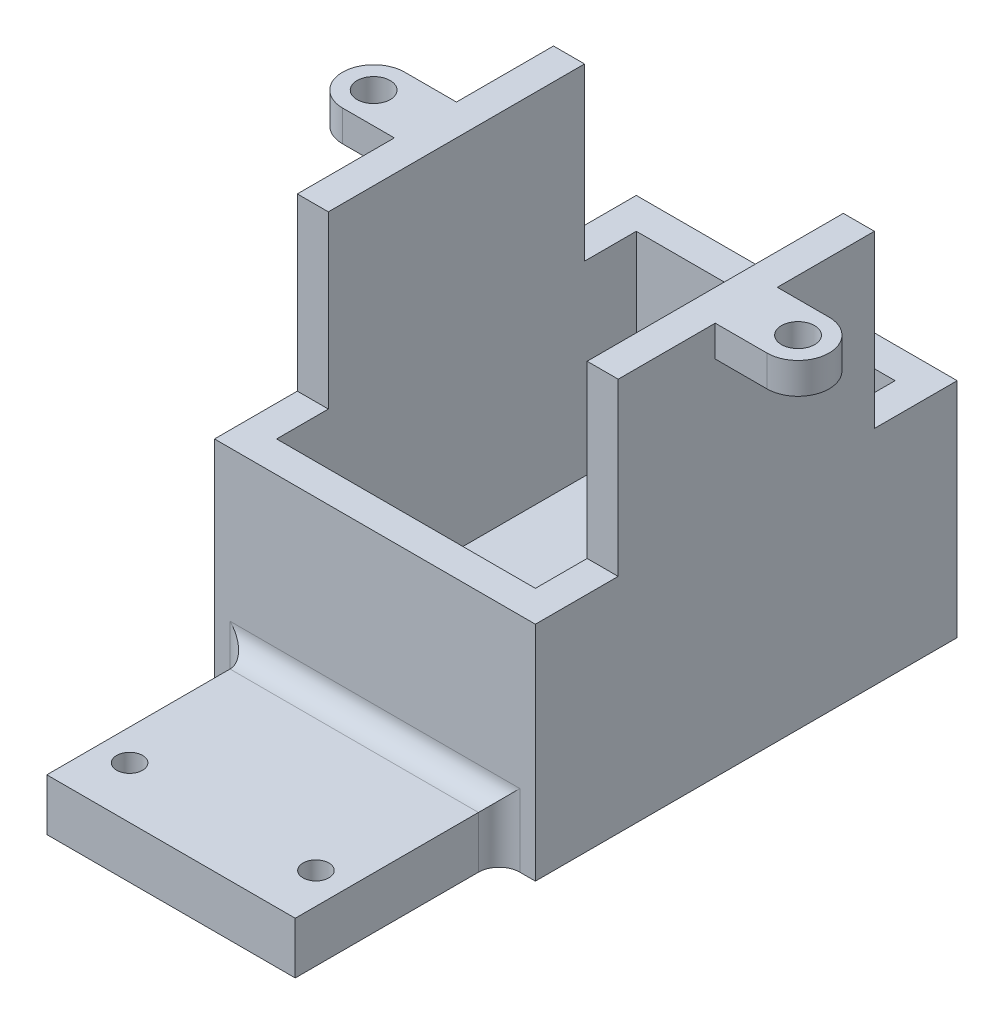
SolidWorks part; units mm, degrees
ref_plane "前视基准面" through (0, 0, 0) normal (0, 0, 1) x (1, 0, 0)
ref_plane "上视基准面" through (0, 0, 0) normal (0, 1, 0) x (1, 0, 0)
ref_plane "右视基准面" through (0, 0, 0) normal (1, 0, 0) x (0, 0, -1)
sketch "草图1" plane through (0, 0, 0) normal (0, 0, 1) x (1, 0, 0)
  line L1 (0, 0) -> (31, 0)
  line L2 (0, 0) -> (0, 38)
  line L3 (0, 38) -> (31, 38)
  line L4 (31, 0) -> (31, 38)
  dimension "D1" = 38
  dimension "D2" = 31
extrude "凸台-拉伸1" add sketch "草图1" against normal blind 40.75
sketch "草图2" plane through (31, 0, 0) normal (1, 0, 0) x (0, 0, -1)
  line L1 (40.75, 38) -> (32.75, 38)
  line L2 (40.75, 38) -> (40.75, 21.5)
  line L3 (40.75, 21.5) -> (32.75, 21.5)
  line L4 (32.75, 38) -> (32.75, 21.5)
  dimension "D1" = 16.5
  dimension "D2" = 8
extrude "切除-拉伸1" cut sketch "草图2" against normal blind 40.75
sketch "草图3" plane through (0, 38, 0) normal (0, 1, 0) x (1, 0, 0)
  line L0 (0, 40.75) -> (31, 0) construction
  line L1 (31, 40.75) -> (0, 40.75) construction
  line L2 (3, 3) -> (28, 3)
  line L3 (3, 3) -> (3, 37.75)
  line L4 (3, 37.75) -> (28, 37.75)
  line L5 (28, 3) -> (28, 37.75)
  line L6 (15.5, 37.75) -> (15.5, 3) construction
  line L7 (3, 20.375) -> (28, 20.375) construction
  line L8 (31, 32.75) -> (31, 0) construction
  point P4 (15.5, 20.375)
  dimension "D1" = 3
  dimension "D2" = 3
extrude "切除-拉伸2" cut sketch "草图3" against normal blind 34.5
sketch "草图4" plane through (0, 0, 0) normal (0, 0, 1) x (1, 0, 0)
  line L0 (31, 38) -> (0, 38) construction
  circle A0 centre (15.5, 38) radius 12.5
  dimension "D1" = 25
extrude "切除-拉伸3" cut sketch "草图4" against normal blind 34.5
sketch "草图5" plane through (0, 38, 0) normal (0, 1, 0) x (1, 0, 0)
  line L0 (0, 40.75) -> (31, 0) construction
  line L1 (15.5, 20.375) -> (15.5, 40.75) construction
  line L2 (15.5, 20.375) -> (31, 20.375) construction
  line L3 (31, 32.75) -> (31, 0) construction
  line L4 (36, 23.375) -> (31, 23.375)
  line L5 (31, 23.375) -> (31, 17.375)
  line L6 (31, 17.375) -> (36, 17.375)
  line L7 (0, 23.375) -> (0, 17.375)
  line L8 (0, 17.375) -> (-5, 17.375)
  line L9 (-5, 23.375) -> (0, 23.375)
  circle A0 centre (36, 20.375) radius 1.6
  arc A1 (36, 17.375) -> (36, 23.375) centre (36, 20.375) ccw
  arc A2 (-5, 17.375) -> (-5, 23.375) centre (-5, 20.375) cw
  circle A3 centre (-5, 20.375) radius 1.6
  dimension "D1" = 3.2
  dimension "D2" = 6
  dimension "D3" = 5
extrude "凸台-拉伸2" add sketch "草图5" against normal blind 3
sketch "草图6" plane through (0, 0, 0) normal (0, 0, 1) x (1, 0, 0)
  line L0 (15.5, 0) -> (15.5, 10.8029) construction
  line L1 (0, 0) -> (31, 0) construction
  line L3 (3.5, 0) -> (27.5, 0)
  line L4 (3.5, 0) -> (3.5, 5)
  line L5 (3.5, 5) -> (27.5, 5)
  line L6 (27.5, 0) -> (27.5, 5)
  dimension "D1" = 24
  dimension "D2" = 5
extrude "凸台-拉伸3" add sketch "草图6" along normal blind 19.7
fillet "圆角1" radius 2 3 edges at (3.5, 2.5, 0) (15.5, 5, 0) (27.5, 2.5, 0)
sketch "草图7" plane through (0, 5, 0) normal (0, 1, 0) x (1, 0, 0)
  circle A0 centre (6.5, -14.7) radius 1.25
  circle A1 centre (24.5, -14.7) radius 1.25
  dimension "D1" = 2.5
  dimension "D2" = 2.5
extrude "切除-拉伸4" cut sketch "草图7" against normal blind 19.7
sketch "草图8" plane through (0, 0, 0) normal (0, 0, 1) x (1, 0, 0)
  line L0 (31, 0) -> (31, 38) construction
  line L1 (0, 38) -> (31, 38)
  line L2 (0, 38) -> (0, 21.5)
  line L3 (0, 21.5) -> (31, 21.5)
  line L4 (31, 38) -> (31, 21.5)
  line L5 (1.5, 0) -> (3.5, 0) construction
  dimension "D1" = 21.5
extrude "切除-拉伸5" cut sketch "草图8" against normal blind 8
